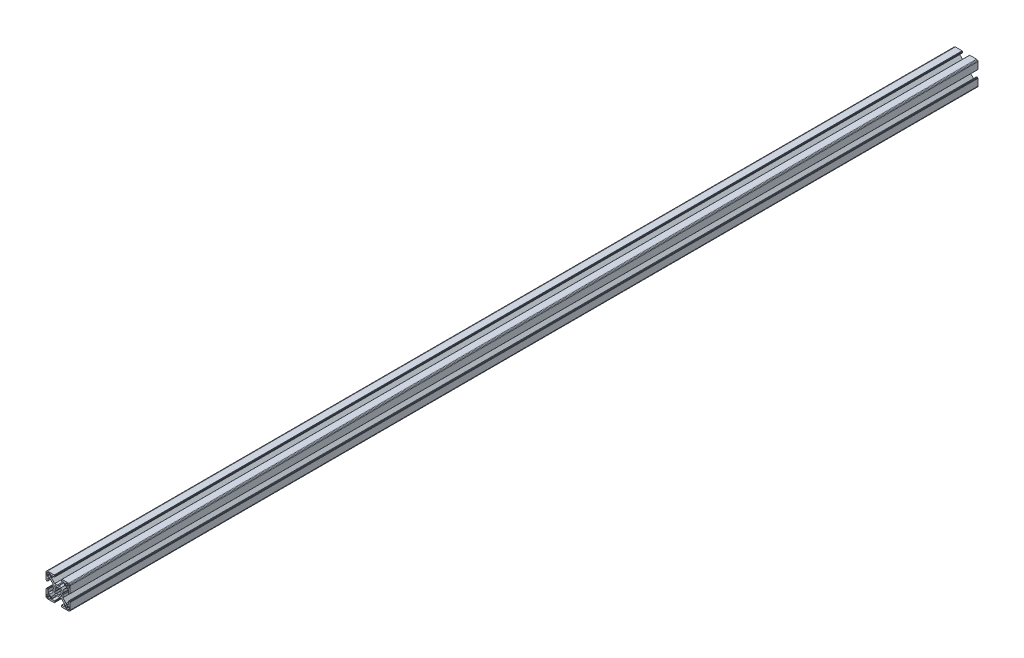
SolidWorks part; units mm, degrees
ref_plane "Front Plane" through (0, 0, 0) normal (0, 0, 1) x (1, 0, 0)
ref_plane "Top Plane" through (0, 0, 0) normal (0, 1, 0) x (1, 0, 0)
ref_plane "Right Plane" through (0, 0, 0) normal (1, 0, 0) x (0, 0, -1)
ref_plane "Plane1" through (0, 0, 0) normal (0, 0, 1) x (1, 0, 0)
sketch "Sketch1" plane through (0, 0, 0) normal (0, 0, 1) x (1, 0, 0)
  line L0 (28.3473, 29.9696) -> (28, 30)
  line L1 (28, 30) -> (19.75, 30)
  line L2 (19.75, 30) -> (19.7153, 29.997)
  line L3 (19.7153, 29.997) -> (19.6816, 29.9879)
  line L4 (19.6816, 29.9879) -> (19.65, 29.9732)
  line L5 (19.65, 29.9732) -> (19.6214, 29.9532)
  line L6 (19.6214, 29.9532) -> (19.5968, 29.9286)
  line L7 (19.5968, 29.9286) -> (19.5768, 29.9)
  line L8 (19.5768, 29.9) -> (19.5621, 29.8684)
  line L9 (19.5621, 29.8684) -> (19.553, 29.8347)
  line L10 (19.553, 29.8347) -> (19.55, 29.8)
  line L11 (19.55, 29.8) -> (19.55, 29.7)
  line L12 (19.55, 29.7) -> (19.547, 29.6653)
  line L13 (19.547, 29.6653) -> (19.5379, 29.6316)
  line L14 (19.5379, 29.6316) -> (19.5232, 29.6)
  line L15 (19.5232, 29.6) -> (19.5032, 29.5714)
  line L16 (19.5032, 29.5714) -> (19.4786, 29.5468)
  line L17 (19.4786, 29.5468) -> (19.45, 29.5268)
  line L18 (19.45, 29.5268) -> (19.4184, 29.5121)
  line L19 (19.4184, 29.5121) -> (19.3847, 29.503)
  line L20 (19.3847, 29.503) -> (19.35, 29.5)
  line L21 (19.35, 29.5) -> (19.25, 29.5)
  line L22 (19.25, 29.5) -> (19.2153, 29.497)
  line L23 (19.2153, 29.497) -> (19.1816, 29.4879)
  line L24 (19.1816, 29.4879) -> (19.15, 29.4732)
  line L25 (19.15, 29.4732) -> (19.1214, 29.4532)
  line L26 (19.1214, 29.4532) -> (19.0968, 29.4286)
  line L27 (19.0968, 29.4286) -> (19.0768, 29.4)
  line L28 (19.0768, 29.4) -> (19.0621, 29.3684)
  line L29 (19.0621, 29.3684) -> (19.053, 29.3347)
  line L30 (19.053, 29.3347) -> (19.05, 29.3)
  line L31 (19.05, 29.3) -> (19.05, 28.4)
  line L32 (19.05, 28.4) -> (19.0591, 28.2958)
  line L33 (19.0591, 28.2958) -> (19.0862, 28.1948)
  line L34 (19.0862, 28.1948) -> (19.1304, 28.1)
  line L35 (19.1304, 28.1) -> (19.1904, 28.0143)
  line L36 (19.1904, 28.0143) -> (19.2643, 27.9404)
  line L37 (19.2643, 27.9404) -> (19.35, 27.8804)
  line L38 (19.35, 27.8804) -> (19.4448, 27.8362)
  line L39 (19.4448, 27.8362) -> (19.5458, 27.8091)
  line L40 (19.5458, 27.8091) -> (19.65, 27.8)
  line L41 (19.65, 27.8) -> (23.05, 27.8)
  line L42 (23.05, 27.8) -> (23.0847, 27.7969)
  line L43 (23.0847, 27.7969) -> (23.1184, 27.7879)
  line L44 (23.1184, 27.7879) -> (23.15, 27.7732)
  line L45 (23.15, 27.7732) -> (23.1786, 27.7532)
  line L46 (23.1786, 27.7532) -> (23.2032, 27.7285)
  line L47 (23.2032, 27.7285) -> (23.2232, 27.7)
  line L48 (23.2232, 27.7) -> (23.2379, 27.6684)
  line L49 (23.2379, 27.6684) -> (23.247, 27.6347)
  line L50 (23.247, 27.6347) -> (23.25, 27.6)
  line L51 (23.25, 27.6) -> (23.25, 25.05)
  line L52 (23.25, 25.05) -> (19.2045, 21)
  line L53 (19.2045, 21) -> (15.9, 21)
  line L54 (15.9, 21) -> (15, 20.4848)
  line L55 (15, 20.4848) -> (14.1, 21)
  line L56 (14.1, 21) -> (10.7955, 21)
  line L57 (10.7955, 21) -> (7.9973, 23.8013)
  line L58 (7.9973, 23.8013) -> (6.75, 25.05)
  line L59 (6.75, 25.05) -> (6.75, 27.6)
  line L60 (6.75, 27.6) -> (6.753, 27.6347)
  line L61 (6.753, 27.6347) -> (6.7621, 27.6684)
  line L62 (6.7621, 27.6684) -> (6.7768, 27.7)
  line L63 (6.7768, 27.7) -> (6.7968, 27.7285)
  line L64 (6.7968, 27.7285) -> (6.8215, 27.7532)
  line L65 (6.8215, 27.7532) -> (6.85, 27.7732)
  line L66 (6.85, 27.7732) -> (6.8816, 27.7879)
  line L67 (6.8816, 27.7879) -> (6.9153, 27.7969)
  line L68 (6.9153, 27.7969) -> (6.95, 27.8)
  line L69 (6.95, 27.8) -> (10.35, 27.8)
  line L70 (10.35, 27.8) -> (10.4542, 27.8091)
  line L71 (10.4542, 27.8091) -> (10.5552, 27.8362)
  line L72 (10.5552, 27.8362) -> (10.65, 27.8804)
  line L73 (10.65, 27.8804) -> (10.7357, 27.9404)
  line L74 (10.7357, 27.9404) -> (10.8096, 28.0143)
  line L75 (10.8096, 28.0143) -> (10.8696, 28.1)
  line L76 (10.8696, 28.1) -> (10.9138, 28.1948)
  line L77 (10.9138, 28.1948) -> (10.9409, 28.2958)
  line L78 (10.9409, 28.2958) -> (10.95, 28.4)
  line L79 (10.95, 28.4) -> (10.95, 29.3)
  line L80 (10.95, 29.3) -> (10.947, 29.3347)
  line L81 (10.947, 29.3347) -> (10.938, 29.3684)
  line L82 (10.938, 29.3684) -> (10.9232, 29.4)
  line L83 (10.9232, 29.4) -> (10.9032, 29.4286)
  line L84 (10.9032, 29.4286) -> (10.8786, 29.4532)
  line L85 (10.8786, 29.4532) -> (10.85, 29.4732)
  line L86 (10.85, 29.4732) -> (10.8184, 29.4879)
  line L87 (10.8184, 29.4879) -> (10.7847, 29.497)
  line L88 (10.7847, 29.497) -> (10.75, 29.5)
  line L89 (10.75, 29.5) -> (10.65, 29.5)
  line L90 (10.65, 29.5) -> (10.6153, 29.503)
  line L91 (10.6153, 29.503) -> (10.5816, 29.5121)
  line L92 (10.5816, 29.5121) -> (10.55, 29.5268)
  line L93 (10.55, 29.5268) -> (10.5214, 29.5468)
  line L94 (10.5214, 29.5468) -> (10.4968, 29.5714)
  line L95 (10.4968, 29.5714) -> (10.4768, 29.6)
  line L96 (10.4768, 29.6) -> (10.4621, 29.6316)
  line L97 (10.4621, 29.6316) -> (10.453, 29.6653)
  line L98 (10.453, 29.6653) -> (10.45, 29.7)
  line L99 (10.45, 29.7) -> (10.45, 29.8)
  line L100 (10.45, 29.8) -> (10.447, 29.8347)
  line L101 (10.447, 29.8347) -> (10.4379, 29.8684)
  line L102 (10.4379, 29.8684) -> (10.4232, 29.9)
  line L103 (10.4232, 29.9) -> (10.4032, 29.9286)
  line L104 (10.4032, 29.9286) -> (10.3786, 29.9532)
  line L105 (10.3786, 29.9532) -> (10.35, 29.9732)
  line L106 (10.35, 29.9732) -> (10.3184, 29.9879)
  line L107 (10.3184, 29.9879) -> (10.2847, 29.997)
  line L108 (10.2847, 29.997) -> (10.25, 30)
  line L109 (10.25, 30) -> (2, 30)
  line L110 (2, 30) -> (1.6527, 29.9696)
  line L111 (1.6527, 29.9696) -> (1.316, 29.8794)
  line L112 (1.316, 29.8794) -> (1, 29.7321)
  line L113 (1, 29.7321) -> (0.7144, 29.5321)
  line L114 (0.7144, 29.5321) -> (0.4679, 29.2856)
  line L115 (0.4679, 29.2856) -> (0.2679, 29)
  line L116 (0.2679, 29) -> (0.1206, 28.684)
  line L117 (0.1206, 28.684) -> (0.0304, 28.3473)
  line L118 (0.0304, 28.3473) -> (0, 28)
  line L119 (0, 28) -> (0, 19.75)
  line L120 (0, 19.75) -> (0.003, 19.7153)
  line L121 (0.003, 19.7153) -> (0.0121, 19.6816)
  line L122 (0.0121, 19.6816) -> (0.0268, 19.65)
  line L123 (0.0268, 19.65) -> (0.0468, 19.6214)
  line L124 (0.0468, 19.6214) -> (0.0714, 19.5968)
  line L125 (0.0714, 19.5968) -> (0.1, 19.5768)
  line L126 (0.1, 19.5768) -> (0.1316, 19.5621)
  line L127 (0.1316, 19.5621) -> (0.1653, 19.553)
  line L128 (0.1653, 19.553) -> (0.2, 19.55)
  line L129 (0.2, 19.55) -> (0.3, 19.55)
  line L130 (0.3, 19.55) -> (0.3347, 19.547)
  line L131 (0.3347, 19.547) -> (0.3684, 19.5379)
  line L132 (0.3684, 19.5379) -> (0.4, 19.5232)
  line L133 (0.4, 19.5232) -> (0.4286, 19.5032)
  line L134 (0.4286, 19.5032) -> (0.4532, 19.4786)
  line L135 (0.4532, 19.4786) -> (0.4732, 19.45)
  line L136 (0.4732, 19.45) -> (0.4879, 19.4184)
  line L137 (0.4879, 19.4184) -> (0.497, 19.3847)
  line L138 (0.497, 19.3847) -> (0.5, 19.35)
  line L139 (0.5, 19.35) -> (0.5, 19.25)
  line L140 (0.5, 19.25) -> (0.503, 19.2153)
  line L141 (0.503, 19.2153) -> (0.5121, 19.1816)
  line L142 (0.5121, 19.1816) -> (0.5268, 19.15)
  line L143 (0.5268, 19.15) -> (0.5468, 19.1214)
  line L144 (0.5468, 19.1214) -> (0.5714, 19.0968)
  line L145 (0.5714, 19.0968) -> (0.6, 19.0768)
  line L146 (0.6, 19.0768) -> (0.6316, 19.0621)
  line L147 (0.6316, 19.0621) -> (0.6653, 19.053)
  line L148 (0.6653, 19.053) -> (0.7, 19.05)
  line L149 (0.7, 19.05) -> (1.6, 19.05)
  line L150 (1.6, 19.05) -> (1.7042, 19.0591)
  line L151 (1.7042, 19.0591) -> (1.8052, 19.0862)
  line L152 (1.8052, 19.0862) -> (1.9, 19.1304)
  line L153 (1.9, 19.1304) -> (1.9857, 19.1904)
  line L154 (1.9857, 19.1904) -> (2.0596, 19.2643)
  line L155 (2.0596, 19.2643) -> (2.1196, 19.35)
  line L156 (2.1196, 19.35) -> (2.1638, 19.4448)
  line L157 (2.1638, 19.4448) -> (2.1909, 19.5458)
  line L158 (2.1909, 19.5458) -> (2.2, 19.65)
  line L159 (2.2, 19.65) -> (2.2, 23.05)
  line L160 (2.2, 23.05) -> (2.203, 23.0847)
  line L161 (2.203, 23.0847) -> (2.2121, 23.1184)
  line L162 (2.2121, 23.1184) -> (2.2268, 23.15)
  line L163 (2.2268, 23.15) -> (2.2468, 23.1786)
  line L164 (2.2468, 23.1786) -> (2.2714, 23.2032)
  line L165 (2.2714, 23.2032) -> (2.3, 23.2232)
  line L166 (2.3, 23.2232) -> (2.3316, 23.2379)
  line L167 (2.3316, 23.2379) -> (2.3653, 23.247)
  line L168 (2.3653, 23.247) -> (2.4, 23.25)
  line L169 (2.4, 23.25) -> (4.95, 23.25)
  line L170 (4.95, 23.25) -> (7.9973, 20.2027)
  line L171 (7.9973, 20.2027) -> (8.9955, 19.2045)
  line L172 (8.9955, 19.2045) -> (8.9955, 15.9)
  line L173 (8.9955, 15.9) -> (9.5151, 15)
  line L174 (9.5151, 15) -> (8.9955, 14.1)
  line L175 (8.9955, 14.1) -> (8.9955, 10.7955)
  line L176 (8.9955, 10.7955) -> (4.95, 6.75)
  line L177 (4.95, 6.75) -> (2.4, 6.75)
  line L178 (2.4, 6.75) -> (2.3653, 6.753)
  line L179 (2.3653, 6.753) -> (2.3316, 6.7621)
  line L180 (2.3316, 6.7621) -> (2.3, 6.7768)
  line L181 (2.3, 6.7768) -> (2.2714, 6.7968)
  line L182 (2.2714, 6.7968) -> (2.2468, 6.8214)
  line L183 (2.2468, 6.8214) -> (2.2268, 6.85)
  line L184 (2.2268, 6.85) -> (2.2121, 6.8816)
  line L185 (2.2121, 6.8816) -> (2.203, 6.9153)
  line L186 (2.203, 6.9153) -> (2.2, 6.95)
  line L187 (2.2, 6.95) -> (2.2, 10.35)
  line L188 (2.2, 10.35) -> (2.1909, 10.4542)
  line L189 (2.1909, 10.4542) -> (2.1638, 10.5552)
  line L190 (2.1638, 10.5552) -> (2.1196, 10.65)
  line L191 (2.1196, 10.65) -> (2.0596, 10.7357)
  line L192 (2.0596, 10.7357) -> (1.9857, 10.8096)
  line L193 (1.9857, 10.8096) -> (1.9, 10.8696)
  line L194 (1.9, 10.8696) -> (1.8052, 10.9138)
  line L195 (1.8052, 10.9138) -> (1.7042, 10.9409)
  line L196 (1.7042, 10.9409) -> (1.6, 10.95)
  line L197 (1.6, 10.95) -> (0.7, 10.95)
  line L198 (0.7, 10.95) -> (0.6653, 10.9469)
  line L199 (0.6653, 10.9469) -> (0.6316, 10.9379)
  line L200 (0.6316, 10.9379) -> (0.6, 10.9232)
  line L201 (0.6, 10.9232) -> (0.5715, 10.9032)
  line L202 (0.5715, 10.9032) -> (0.5468, 10.8785)
  line L203 (0.5468, 10.8785) -> (0.5268, 10.85)
  line L204 (0.5268, 10.85) -> (0.5121, 10.8184)
  line L205 (0.5121, 10.8184) -> (0.503, 10.7847)
  line L206 (0.503, 10.7847) -> (0.5, 10.75)
  line L207 (0.5, 10.75) -> (0.5, 10.65)
  line L208 (0.5, 10.65) -> (0.497, 10.6153)
  line L209 (0.497, 10.6153) -> (0.4879, 10.5816)
  line L210 (0.4879, 10.5816) -> (0.4732, 10.55)
  line L211 (0.4732, 10.55) -> (0.4532, 10.5214)
  line L212 (0.4532, 10.5214) -> (0.4286, 10.4968)
  line L213 (0.4286, 10.4968) -> (0.4, 10.4768)
  line L214 (0.4, 10.4768) -> (0.3684, 10.4621)
  line L215 (0.3684, 10.4621) -> (0.3347, 10.453)
  line L216 (0.3347, 10.453) -> (0.3, 10.45)
  line L217 (0.3, 10.45) -> (0.2, 10.45)
  line L218 (0.2, 10.45) -> (0.1653, 10.447)
  line L219 (0.1653, 10.447) -> (0.1316, 10.4379)
  line L220 (0.1316, 10.4379) -> (0.1, 10.4232)
  line L221 (0.1, 10.4232) -> (0.0714, 10.4032)
  line L222 (0.0714, 10.4032) -> (0.0468, 10.3786)
  line L223 (0.0468, 10.3786) -> (0.0268, 10.35)
  line L224 (0.0268, 10.35) -> (0.0121, 10.3184)
  line L225 (0.0121, 10.3184) -> (0.003, 10.2847)
  line L226 (0.003, 10.2847) -> (0, 10.25)
  line L227 (0, 10.25) -> (0, 2)
  line L228 (0, 2) -> (0.0304, 1.6527)
  line L229 (0.0304, 1.6527) -> (0.1206, 1.316)
  line L230 (0.1206, 1.316) -> (0.2679, 1)
  line L231 (0.2679, 1) -> (0.4679, 0.7144)
  line L232 (0.4679, 0.7144) -> (0.7144, 0.4679)
  line L233 (0.7144, 0.4679) -> (1, 0.2679)
  line L234 (1, 0.2679) -> (1.316, 0.1206)
  line L235 (1.316, 0.1206) -> (1.6527, 0.0304)
  line L236 (1.6527, 0.0304) -> (2, 0)
  line L237 (2, 0) -> (10.25, 0)
  line L238 (10.25, 0) -> (10.2847, 0.003)
  line L239 (10.2847, 0.003) -> (10.3184, 0.0121)
  line L240 (10.3184, 0.0121) -> (10.35, 0.0268)
  line L241 (10.35, 0.0268) -> (10.3786, 0.0468)
  line L242 (10.3786, 0.0468) -> (10.4032, 0.0714)
  line L243 (10.4032, 0.0714) -> (10.4232, 0.1)
  line L244 (10.4232, 0.1) -> (10.4379, 0.1316)
  line L245 (10.4379, 0.1316) -> (10.447, 0.1653)
  line L246 (10.447, 0.1653) -> (10.45, 0.2)
  line L247 (10.45, 0.2) -> (10.45, 0.3)
  line L248 (10.45, 0.3) -> (10.453, 0.3347)
  line L249 (10.453, 0.3347) -> (10.4621, 0.3684)
  line L250 (10.4621, 0.3684) -> (10.4768, 0.4)
  line L251 (10.4768, 0.4) -> (10.4968, 0.4286)
  line L252 (10.4968, 0.4286) -> (10.5214, 0.4532)
  line L253 (10.5214, 0.4532) -> (10.55, 0.4732)
  line L254 (10.55, 0.4732) -> (10.5816, 0.4879)
  line L255 (10.5816, 0.4879) -> (10.6153, 0.497)
  line L256 (10.6153, 0.497) -> (10.65, 0.5)
  line L257 (10.65, 0.5) -> (10.75, 0.5)
  line L258 (10.75, 0.5) -> (10.7847, 0.503)
  line L259 (10.7847, 0.503) -> (10.8184, 0.5121)
  line L260 (10.8184, 0.5121) -> (10.85, 0.5268)
  line L261 (10.85, 0.5268) -> (10.8785, 0.5468)
  line L262 (10.8785, 0.5468) -> (10.9032, 0.5715)
  line L263 (10.9032, 0.5715) -> (10.9232, 0.6)
  line L264 (10.9232, 0.6) -> (10.9379, 0.6316)
  line L265 (10.9379, 0.6316) -> (10.9469, 0.6653)
  line L266 (10.9469, 0.6653) -> (10.95, 0.7)
  line L267 (10.95, 0.7) -> (10.95, 1.6)
  line L268 (10.95, 1.6) -> (10.9409, 1.7042)
  line L269 (10.9409, 1.7042) -> (10.9138, 1.8052)
  line L270 (10.9138, 1.8052) -> (10.8696, 1.9)
  line L271 (10.8696, 1.9) -> (10.8096, 1.9857)
  line L272 (10.8096, 1.9857) -> (10.7357, 2.0596)
  line L273 (10.7357, 2.0596) -> (10.65, 2.1196)
  line L274 (10.65, 2.1196) -> (10.5552, 2.1638)
  line L275 (10.5552, 2.1638) -> (10.4542, 2.1909)
  line L276 (10.4542, 2.1909) -> (10.35, 2.2)
  line L277 (10.35, 2.2) -> (6.95, 2.2)
  line L278 (6.95, 2.2) -> (6.9153, 2.203)
  line L279 (6.9153, 2.203) -> (6.8816, 2.212)
  line L280 (6.8816, 2.212) -> (6.85, 2.2268)
  line L281 (6.85, 2.2268) -> (6.8215, 2.2468)
  line L282 (6.8215, 2.2468) -> (6.7968, 2.2714)
  line L283 (6.7968, 2.2714) -> (6.7768, 2.3)
  line L284 (6.7768, 2.3) -> (6.7621, 2.3316)
  line L285 (6.7621, 2.3316) -> (6.753, 2.3653)
  line L286 (6.753, 2.3653) -> (6.75, 2.4)
  line L287 (6.75, 2.4) -> (6.75, 4.95)
  line L288 (6.75, 4.95) -> (9.7875, 7.9908)
  line L289 (9.7875, 7.9908) -> (10.7955, 9)
  line L290 (10.7955, 9) -> (14.1, 9)
  line L291 (14.1, 9) -> (15, 9.5151)
  line L292 (15, 9.5151) -> (15.9, 9)
  line L293 (15.9, 9) -> (19.2045, 9)
  line L294 (19.2045, 9) -> (20.2126, 7.9908)
  line L295 (20.2126, 7.9908) -> (23.25, 4.95)
  line L296 (23.25, 4.95) -> (23.25, 2.4)
  line L297 (23.25, 2.4) -> (23.247, 2.3653)
  line L298 (23.247, 2.3653) -> (23.2379, 2.3316)
  line L299 (23.2379, 2.3316) -> (23.2232, 2.3)
  line L300 (23.2232, 2.3) -> (23.2032, 2.2714)
  line L301 (23.2032, 2.2714) -> (23.1786, 2.2468)
  line L302 (23.1786, 2.2468) -> (23.15, 2.2268)
  line L303 (23.15, 2.2268) -> (23.1184, 2.212)
  line L304 (23.1184, 2.212) -> (23.0847, 2.203)
  line L305 (23.0847, 2.203) -> (23.05, 2.2)
  line L306 (23.05, 2.2) -> (19.65, 2.2)
  line L307 (19.65, 2.2) -> (19.5458, 2.1909)
  line L308 (19.5458, 2.1909) -> (19.4448, 2.1638)
  line L309 (19.4448, 2.1638) -> (19.35, 2.1196)
  line L310 (19.35, 2.1196) -> (19.2643, 2.0596)
  line L311 (19.2643, 2.0596) -> (19.1904, 1.9857)
  line L312 (19.1904, 1.9857) -> (19.1304, 1.9)
  line L313 (19.1304, 1.9) -> (19.0862, 1.8052)
  line L314 (19.0862, 1.8052) -> (19.0591, 1.7042)
  line L315 (19.0591, 1.7042) -> (19.05, 1.6)
  line L316 (19.05, 1.6) -> (19.05, 0.7)
  line L317 (19.05, 0.7) -> (19.053, 0.6653)
  line L318 (19.053, 0.6653) -> (19.0621, 0.6316)
  line L319 (19.0621, 0.6316) -> (19.0768, 0.6)
  line L320 (19.0768, 0.6) -> (19.0968, 0.5714)
  line L321 (19.0968, 0.5714) -> (19.1214, 0.5468)
  line L322 (19.1214, 0.5468) -> (19.15, 0.5268)
  line L323 (19.15, 0.5268) -> (19.1816, 0.5121)
  line L324 (19.1816, 0.5121) -> (19.2153, 0.503)
  line L325 (19.2153, 0.503) -> (19.25, 0.5)
  line L326 (19.25, 0.5) -> (19.35, 0.5)
  line L327 (19.35, 0.5) -> (19.3847, 0.497)
  line L328 (19.3847, 0.497) -> (19.4184, 0.4879)
  line L329 (19.4184, 0.4879) -> (19.45, 0.4732)
  line L330 (19.45, 0.4732) -> (19.4786, 0.4532)
  line L331 (19.4786, 0.4532) -> (19.5032, 0.4286)
  line L332 (19.5032, 0.4286) -> (19.5232, 0.4)
  line L333 (19.5232, 0.4) -> (19.5379, 0.3684)
  line L334 (19.5379, 0.3684) -> (19.547, 0.3347)
  line L335 (19.547, 0.3347) -> (19.55, 0.3)
  line L336 (19.55, 0.3) -> (19.55, 0.2)
  line L337 (19.55, 0.2) -> (19.553, 0.1653)
  line L338 (19.553, 0.1653) -> (19.5621, 0.1316)
  line L339 (19.5621, 0.1316) -> (19.5768, 0.1)
  line L340 (19.5768, 0.1) -> (19.5968, 0.0714)
  line L341 (19.5968, 0.0714) -> (19.6214, 0.0468)
  line L342 (19.6214, 0.0468) -> (19.65, 0.0268)
  line L343 (19.65, 0.0268) -> (19.6816, 0.0121)
  line L344 (19.6816, 0.0121) -> (19.7153, 0.003)
  line L345 (19.7153, 0.003) -> (19.75, 0)
  line L346 (19.75, 0) -> (28, 0)
  line L347 (28, 0) -> (28.3473, 0.0304)
  line L348 (28.3473, 0.0304) -> (28.684, 0.1206)
  line L349 (28.684, 0.1206) -> (29, 0.2679)
  line L350 (29, 0.2679) -> (29.2856, 0.4679)
  line L351 (29.2856, 0.4679) -> (29.5321, 0.7144)
  line L352 (29.5321, 0.7144) -> (29.7321, 1)
  line L353 (29.7321, 1) -> (29.8794, 1.316)
  line L354 (29.8794, 1.316) -> (29.9696, 1.6527)
  line L355 (29.9696, 1.6527) -> (30, 2)
  line L356 (30, 2) -> (30, 10.25)
  line L357 (30, 10.25) -> (29.997, 10.2847)
  line L358 (29.997, 10.2847) -> (29.988, 10.3184)
  line L359 (29.988, 10.3184) -> (29.9732, 10.35)
  line L360 (29.9732, 10.35) -> (29.9532, 10.3785)
  line L361 (29.9532, 10.3785) -> (29.9286, 10.4032)
  line L362 (29.9286, 10.4032) -> (29.9, 10.4232)
  line L363 (29.9, 10.4232) -> (29.8684, 10.4379)
  line L364 (29.8684, 10.4379) -> (29.8347, 10.447)
  line L365 (29.8347, 10.447) -> (29.8, 10.45)
  line L366 (29.8, 10.45) -> (29.7, 10.45)
  line L367 (29.7, 10.45) -> (29.6649, 10.4534)
  line L368 (29.6649, 10.4534) -> (29.6312, 10.4624)
  line L369 (29.6312, 10.4624) -> (29.5996, 10.4772)
  line L370 (29.5996, 10.4772) -> (29.5711, 10.4972)
  line L371 (29.5711, 10.4972) -> (29.5464, 10.5218)
  line L372 (29.5464, 10.5218) -> (29.5264, 10.5504)
  line L373 (29.5264, 10.5504) -> (29.5117, 10.582)
  line L374 (29.5117, 10.582) -> (29.5027, 10.6156)
  line L375 (29.5027, 10.6156) -> (29.4996, 10.6504)
  line L376 (29.4996, 10.6504) -> (29.4996, 10.7504)
  line L377 (29.4996, 10.7504) -> (29.497, 10.7847)
  line L378 (29.497, 10.7847) -> (29.4879, 10.8184)
  line L379 (29.4879, 10.8184) -> (29.4732, 10.85)
  line L380 (29.4732, 10.85) -> (29.4532, 10.8785)
  line L381 (29.4532, 10.8785) -> (29.4286, 10.9032)
  line L382 (29.4286, 10.9032) -> (29.4, 10.9232)
  line L383 (29.4, 10.9232) -> (29.3684, 10.9379)
  line L384 (29.3684, 10.9379) -> (29.3347, 10.9469)
  line L385 (29.3347, 10.9469) -> (29.3, 10.95)
  line L386 (29.3, 10.95) -> (28.4, 10.95)
  line L387 (28.4, 10.95) -> (28.2958, 10.9409)
  line L388 (28.2958, 10.9409) -> (28.1948, 10.9138)
  line L389 (28.1948, 10.9138) -> (28.1, 10.8696)
  line L390 (28.1, 10.8696) -> (28.0143, 10.8096)
  line L391 (28.0143, 10.8096) -> (27.9404, 10.7357)
  line L392 (27.9404, 10.7357) -> (27.8804, 10.65)
  line L393 (27.8804, 10.65) -> (27.8362, 10.5552)
  line L394 (27.8362, 10.5552) -> (27.8091, 10.4542)
  line L395 (27.8091, 10.4542) -> (27.8, 10.35)
  line L396 (27.8, 10.35) -> (27.8, 6.95)
  line L397 (27.8, 6.95) -> (27.797, 6.9153)
  line L398 (27.797, 6.9153) -> (27.7879, 6.8816)
  line L399 (27.7879, 6.8816) -> (27.7732, 6.85)
  line L400 (27.7732, 6.85) -> (27.7532, 6.8214)
  line L401 (27.7532, 6.8214) -> (27.7286, 6.7968)
  line L402 (27.7286, 6.7968) -> (27.7, 6.7768)
  line L403 (27.7, 6.7768) -> (27.6684, 6.7621)
  line L404 (27.6684, 6.7621) -> (27.6347, 6.753)
  line L405 (27.6347, 6.753) -> (27.6, 6.75)
  line L406 (27.6, 6.75) -> (25.05, 6.75)
  line L407 (25.05, 6.75) -> (23.8092, 7.9908)
  line L408 (23.8092, 7.9908) -> (21.0045, 10.7955)
  line L409 (21.0045, 10.7955) -> (21.0045, 14.1)
  line L410 (21.0045, 14.1) -> (20.4849, 15)
  line L411 (20.4849, 15) -> (21.0045, 15.9)
  line L412 (21.0045, 15.9) -> (21.0045, 19.2045)
  line L413 (21.0045, 19.2045) -> (25.05, 23.25)
  line L414 (25.05, 23.25) -> (27.6, 23.25)
  line L415 (27.6, 23.25) -> (27.6347, 23.247)
  line L416 (27.6347, 23.247) -> (27.6684, 23.2379)
  line L417 (27.6684, 23.2379) -> (27.7, 23.2232)
  line L418 (27.7, 23.2232) -> (27.7286, 23.2032)
  line L419 (27.7286, 23.2032) -> (27.7532, 23.1786)
  line L420 (27.7532, 23.1786) -> (27.7732, 23.15)
  line L421 (27.7732, 23.15) -> (27.7879, 23.1184)
  line L422 (27.7879, 23.1184) -> (27.797, 23.0847)
  line L423 (27.797, 23.0847) -> (27.8, 23.05)
  line L424 (27.8, 23.05) -> (27.8, 19.65)
  line L425 (27.8, 19.65) -> (27.8091, 19.5458)
  line L426 (27.8091, 19.5458) -> (27.8362, 19.4448)
  line L427 (27.8362, 19.4448) -> (27.8804, 19.35)
  line L428 (27.8804, 19.35) -> (27.9404, 19.2643)
  line L429 (27.9404, 19.2643) -> (28.0143, 19.1904)
  line L430 (28.0143, 19.1904) -> (28.1, 19.1304)
  line L431 (28.1, 19.1304) -> (28.1948, 19.0862)
  line L432 (28.1948, 19.0862) -> (28.2958, 19.0591)
  line L433 (28.2958, 19.0591) -> (28.4, 19.05)
  line L434 (28.4, 19.05) -> (29.3, 19.05)
  line L435 (29.3, 19.05) -> (29.3347, 19.053)
  line L436 (29.3347, 19.053) -> (29.3684, 19.0621)
  line L437 (29.3684, 19.0621) -> (29.4, 19.0768)
  line L438 (29.4, 19.0768) -> (29.4282, 19.0971)
  line L439 (29.4282, 19.0971) -> (29.4528, 19.1218)
  line L440 (29.4528, 19.1218) -> (29.4728, 19.1504)
  line L441 (29.4728, 19.1504) -> (29.4876, 19.182)
  line L442 (29.4876, 19.182) -> (29.4966, 19.2156)
  line L443 (29.4966, 19.2156) -> (29.4996, 19.2504)
  line L444 (29.4996, 19.2504) -> (29.4996, 19.3504)
  line L445 (29.4996, 19.3504) -> (29.5027, 19.3851)
  line L446 (29.5027, 19.3851) -> (29.5117, 19.4188)
  line L447 (29.5117, 19.4188) -> (29.5264, 19.4504)
  line L448 (29.5264, 19.4504) -> (29.5464, 19.4789)
  line L449 (29.5464, 19.4789) -> (29.5711, 19.5036)
  line L450 (29.5711, 19.5036) -> (29.5996, 19.5236)
  line L451 (29.5996, 19.5236) -> (29.6312, 19.5383)
  line L452 (29.6312, 19.5383) -> (29.6649, 19.5473)
  line L453 (29.6649, 19.5473) -> (29.7, 19.55)
  line L454 (29.7, 19.55) -> (29.8, 19.55)
  line L455 (29.8, 19.55) -> (29.8347, 19.553)
  line L456 (29.8347, 19.553) -> (29.8684, 19.5621)
  line L457 (29.8684, 19.5621) -> (29.9, 19.5768)
  line L458 (29.9, 19.5768) -> (29.9286, 19.5968)
  line L459 (29.9286, 19.5968) -> (29.9532, 19.6214)
  line L460 (29.9532, 19.6214) -> (29.9732, 19.65)
  line L461 (29.9732, 19.65) -> (29.9879, 19.6816)
  line L462 (29.9879, 19.6816) -> (29.997, 19.7153)
  line L463 (29.997, 19.7153) -> (30, 19.75)
  line L464 (30, 19.75) -> (30, 28)
  line L465 (30, 28) -> (29.9696, 28.3473)
  line L466 (29.9696, 28.3473) -> (29.8794, 28.684)
  line L467 (29.8794, 28.684) -> (29.7321, 29)
  line L468 (29.7321, 29) -> (29.5321, 29.2856)
  line L469 (29.5321, 29.2856) -> (29.2856, 29.5321)
  line L470 (29.2856, 29.5321) -> (29, 29.7321)
  line L471 (29, 29.7321) -> (28.684, 29.8794)
  line L472 (28.684, 29.8794) -> (28.3473, 29.9696)
  line L473 (1.3, 25.5) -> (1.3, 27.7)
  line L474 (1.3, 27.7) -> (1.3123, 27.8564)
  line L475 (1.3123, 27.8564) -> (1.3489, 28.009)
  line L476 (1.3489, 28.009) -> (1.409, 28.154)
  line L477 (1.409, 28.154) -> (1.491, 28.2878)
  line L478 (1.491, 28.2878) -> (1.5929, 28.4071)
  line L479 (1.5929, 28.4071) -> (1.7122, 28.509)
  line L480 (1.7122, 28.509) -> (1.846, 28.591)
  line L481 (1.846, 28.591) -> (1.991, 28.6511)
  line L482 (1.991, 28.6511) -> (2.1436, 28.6877)
  line L483 (2.1436, 28.6877) -> (2.3, 28.7)
  line L484 (2.3, 28.7) -> (4.5, 28.7)
  line L485 (4.5, 28.7) -> (4.6564, 28.6877)
  line L486 (4.6564, 28.6877) -> (4.809, 28.6511)
  line L487 (4.809, 28.6511) -> (4.954, 28.591)
  line L488 (4.954, 28.591) -> (5.0878, 28.509)
  line L489 (5.0878, 28.509) -> (5.2071, 28.4071)
  line L490 (5.2071, 28.4071) -> (5.309, 28.2878)
  line L491 (5.309, 28.2878) -> (5.391, 28.154)
  line L492 (5.391, 28.154) -> (5.4511, 28.009)
  line L493 (5.4511, 28.009) -> (5.4877, 27.8564)
  line L494 (5.4877, 27.8564) -> (5.5, 27.7)
  line L495 (5.5, 27.7) -> (5.5, 25.5)
  line L496 (5.5, 25.5) -> (5.4877, 25.3436)
  line L497 (5.4877, 25.3436) -> (5.4511, 25.191)
  line L498 (5.4511, 25.191) -> (5.391, 25.046)
  line L499 (5.391, 25.046) -> (5.309, 24.9122)
  line L500 (5.309, 24.9122) -> (5.2071, 24.7929)
  line L501 (5.2071, 24.7929) -> (5.0878, 24.691)
  line L502 (5.0878, 24.691) -> (4.954, 24.609)
  line L503 (4.954, 24.609) -> (4.809, 24.5489)
  line L504 (4.809, 24.5489) -> (4.6564, 24.5123)
  line L505 (4.6564, 24.5123) -> (4.5, 24.5)
  line L506 (4.5, 24.5) -> (2.3, 24.5)
  line L507 (2.3, 24.5) -> (2.1436, 24.5123)
  line L508 (2.1436, 24.5123) -> (1.991, 24.5489)
  line L509 (1.991, 24.5489) -> (1.846, 24.609)
  line L510 (1.846, 24.609) -> (1.7122, 24.691)
  line L511 (1.7122, 24.691) -> (1.5929, 24.7929)
  line L512 (1.5929, 24.7929) -> (1.491, 24.9122)
  line L513 (1.491, 24.9122) -> (1.409, 25.046)
  line L514 (1.409, 25.046) -> (1.3489, 25.191)
  line L515 (1.3489, 25.191) -> (1.3123, 25.3436)
  line L516 (1.3123, 25.3436) -> (1.3, 25.5)
  line L517 (25.3436, 28.6877) -> (25.5, 28.7)
  line L518 (25.5, 28.7) -> (27.7, 28.7)
  line L519 (27.7, 28.7) -> (27.8564, 28.6877)
  line L520 (27.8564, 28.6877) -> (28.009, 28.6511)
  line L521 (28.009, 28.6511) -> (28.154, 28.591)
  line L522 (28.154, 28.591) -> (28.2878, 28.509)
  line L523 (28.2878, 28.509) -> (28.4071, 28.4071)
  line L524 (28.4071, 28.4071) -> (28.509, 28.2878)
  line L525 (28.509, 28.2878) -> (28.591, 28.154)
  line L526 (28.591, 28.154) -> (28.6511, 28.009)
  line L527 (28.6511, 28.009) -> (28.6877, 27.8564)
  line L528 (28.6877, 27.8564) -> (28.7, 27.7)
  line L529 (28.7, 27.7) -> (28.7, 25.5)
  line L530 (28.7, 25.5) -> (28.6877, 25.3436)
  line L531 (28.6877, 25.3436) -> (28.6511, 25.191)
  line L532 (28.6511, 25.191) -> (28.591, 25.046)
  line L533 (28.591, 25.046) -> (28.509, 24.9122)
  line L534 (28.509, 24.9122) -> (28.4071, 24.7929)
  line L535 (28.4071, 24.7929) -> (28.2878, 24.691)
  line L536 (28.2878, 24.691) -> (28.154, 24.609)
  line L537 (28.154, 24.609) -> (28.009, 24.5489)
  line L538 (28.009, 24.5489) -> (27.8564, 24.5123)
  line L539 (27.8564, 24.5123) -> (27.7, 24.5)
  line L540 (27.7, 24.5) -> (25.5, 24.5)
  line L541 (25.5, 24.5) -> (25.3436, 24.5123)
  line L542 (25.3436, 24.5123) -> (25.191, 24.5489)
  line L543 (25.191, 24.5489) -> (25.046, 24.609)
  line L544 (25.046, 24.609) -> (24.9122, 24.691)
  line L545 (24.9122, 24.691) -> (24.7929, 24.7929)
  line L546 (24.7929, 24.7929) -> (24.691, 24.9122)
  line L547 (24.691, 24.9122) -> (24.609, 25.046)
  line L548 (24.609, 25.046) -> (24.5489, 25.191)
  line L549 (24.5489, 25.191) -> (24.5123, 25.3436)
  line L550 (24.5123, 25.3436) -> (24.5, 25.5)
  line L551 (24.5, 25.5) -> (24.5, 27.7)
  line L552 (24.5, 27.7) -> (24.5123, 27.8564)
  line L553 (24.5123, 27.8564) -> (24.5489, 28.009)
  line L554 (24.5489, 28.009) -> (24.609, 28.154)
  line L555 (24.609, 28.154) -> (24.691, 28.2878)
  line L556 (24.691, 28.2878) -> (24.7929, 28.4071)
  line L557 (24.7929, 28.4071) -> (24.9122, 28.509)
  line L558 (24.9122, 28.509) -> (25.046, 28.591)
  line L559 (25.046, 28.591) -> (25.191, 28.6511)
  line L560 (25.191, 28.6511) -> (25.3436, 28.6877)
  line L561 (15, 18.65) -> (15.55, 18.6083)
  line L562 (15.55, 18.6083) -> (16.0875, 18.4842)
  line L563 (16.0875, 18.4842) -> (16.6001, 18.2806)
  line L564 (16.6001, 18.2806) -> (18.1359, 19.5184)
  line L565 (18.1359, 19.5184) -> (18.645, 19.1187)
  line L566 (18.645, 19.1187) -> (19.1036, 18.6621)
  line L567 (19.1036, 18.6621) -> (19.5053, 18.1547)
  line L568 (19.5053, 18.1547) -> (18.2806, 16.6001)
  line L569 (18.2806, 16.6001) -> (18.4842, 16.0875)
  line L570 (18.4842, 16.0875) -> (18.6083, 15.55)
  line L571 (18.6083, 15.55) -> (18.65, 15)
  line L572 (18.65, 15) -> (18.6083, 14.45)
  line L573 (18.6083, 14.45) -> (18.4842, 13.9125)
  line L574 (18.4842, 13.9125) -> (18.2806, 13.3999)
  line L575 (18.2806, 13.3999) -> (19.5053, 11.8453)
  line L576 (19.5053, 11.8453) -> (19.1036, 11.3379)
  line L577 (19.1036, 11.3379) -> (18.645, 10.8813)
  line L578 (18.645, 10.8813) -> (18.1359, 10.4816)
  line L579 (18.1359, 10.4816) -> (16.6001, 11.7194)
  line L580 (16.6001, 11.7194) -> (16.0875, 11.5158)
  line L581 (16.0875, 11.5158) -> (15.55, 11.3917)
  line L582 (15.55, 11.3917) -> (15, 11.35)
  line L583 (15, 11.35) -> (14.45, 11.3917)
  line L584 (14.45, 11.3917) -> (13.9125, 11.5158)
  line L585 (13.9125, 11.5158) -> (13.3999, 11.7194)
  line L586 (13.3999, 11.7194) -> (11.8641, 10.4816)
  line L587 (11.8641, 10.4816) -> (11.355, 10.8813)
  line L588 (11.355, 10.8813) -> (10.8964, 11.3379)
  line L589 (10.8964, 11.3379) -> (10.4947, 11.8453)
  line L590 (10.4947, 11.8453) -> (11.7194, 13.3999)
  line L591 (11.7194, 13.3999) -> (11.5158, 13.9125)
  line L592 (11.5158, 13.9125) -> (11.3917, 14.45)
  line L593 (11.3917, 14.45) -> (11.35, 15)
  line L594 (11.35, 15) -> (11.3917, 15.55)
  line L595 (11.3917, 15.55) -> (11.5158, 16.0875)
  line L596 (11.5158, 16.0875) -> (11.7194, 16.6001)
  line L597 (11.7194, 16.6001) -> (10.4947, 18.1547)
  line L598 (10.4947, 18.1547) -> (10.8964, 18.6621)
  line L599 (10.8964, 18.6621) -> (11.355, 19.1187)
  line L600 (11.355, 19.1187) -> (11.8641, 19.5184)
  line L601 (11.8641, 19.5184) -> (13.3999, 18.2806)
  line L602 (13.3999, 18.2806) -> (13.9125, 18.4842)
  line L603 (13.9125, 18.4842) -> (14.45, 18.6083)
  line L604 (14.45, 18.6083) -> (15, 18.65)
  line L605 (4.5, 1.3) -> (2.3, 1.3)
  line L606 (2.3, 1.3) -> (2.1436, 1.3123)
  line L607 (2.1436, 1.3123) -> (1.991, 1.3489)
  line L608 (1.991, 1.3489) -> (1.846, 1.409)
  line L609 (1.846, 1.409) -> (1.7122, 1.491)
  line L610 (1.7122, 1.491) -> (1.5929, 1.5929)
  line L611 (1.5929, 1.5929) -> (1.491, 1.7122)
  line L612 (1.491, 1.7122) -> (1.409, 1.846)
  line L613 (1.409, 1.846) -> (1.3489, 1.991)
  line L614 (1.3489, 1.991) -> (1.3123, 2.1436)
  line L615 (1.3123, 2.1436) -> (1.3, 2.3)
  line L616 (1.3, 2.3) -> (1.3, 4.5)
  line L617 (1.3, 4.5) -> (1.3123, 4.6564)
  line L618 (1.3123, 4.6564) -> (1.3489, 4.809)
  line L619 (1.3489, 4.809) -> (1.409, 4.954)
  line L620 (1.409, 4.954) -> (1.491, 5.0878)
  line L621 (1.491, 5.0878) -> (1.5929, 5.2071)
  line L622 (1.5929, 5.2071) -> (1.7122, 5.309)
  line L623 (1.7122, 5.309) -> (1.846, 5.391)
  line L624 (1.846, 5.391) -> (1.991, 5.4511)
  line L625 (1.991, 5.4511) -> (2.1436, 5.4877)
  line L626 (2.1436, 5.4877) -> (2.3, 5.5)
  line L627 (2.3, 5.5) -> (4.5, 5.5)
  line L628 (4.5, 5.5) -> (4.6564, 5.4877)
  line L629 (4.6564, 5.4877) -> (4.809, 5.4511)
  line L630 (4.809, 5.4511) -> (4.954, 5.391)
  line L631 (4.954, 5.391) -> (5.0878, 5.309)
  line L632 (5.0878, 5.309) -> (5.2071, 5.2071)
  line L633 (5.2071, 5.2071) -> (5.309, 5.0878)
  line L634 (5.309, 5.0878) -> (5.391, 4.954)
  line L635 (5.391, 4.954) -> (5.4511, 4.809)
  line L636 (5.4511, 4.809) -> (5.4877, 4.6564)
  line L637 (5.4877, 4.6564) -> (5.5, 4.5)
  line L638 (5.5, 4.5) -> (5.5, 2.3)
  line L639 (5.5, 2.3) -> (5.4877, 2.1436)
  line L640 (5.4877, 2.1436) -> (5.4511, 1.991)
  line L641 (5.4511, 1.991) -> (5.391, 1.846)
  line L642 (5.391, 1.846) -> (5.309, 1.7122)
  line L643 (5.309, 1.7122) -> (5.2071, 1.5929)
  line L644 (5.2071, 1.5929) -> (5.0878, 1.491)
  line L645 (5.0878, 1.491) -> (4.954, 1.409)
  line L646 (4.954, 1.409) -> (4.809, 1.3489)
  line L647 (4.809, 1.3489) -> (4.6564, 1.3123)
  line L648 (4.6564, 1.3123) -> (4.5, 1.3)
  line L649 (27.7, 1.3) -> (25.5, 1.3)
  line L650 (25.5, 1.3) -> (25.3436, 1.3123)
  line L651 (25.3436, 1.3123) -> (25.191, 1.3489)
  line L652 (25.191, 1.3489) -> (25.046, 1.409)
  line L653 (25.046, 1.409) -> (24.9122, 1.491)
  line L654 (24.9122, 1.491) -> (24.7929, 1.5929)
  line L655 (24.7929, 1.5929) -> (24.691, 1.7122)
  line L656 (24.691, 1.7122) -> (24.609, 1.846)
  line L657 (24.609, 1.846) -> (24.5489, 1.991)
  line L658 (24.5489, 1.991) -> (24.5123, 2.1436)
  line L659 (24.5123, 2.1436) -> (24.5, 2.3)
  line L660 (24.5, 2.3) -> (24.5, 4.5)
  line L661 (24.5, 4.5) -> (24.5123, 4.6564)
  line L662 (24.5123, 4.6564) -> (24.5489, 4.809)
  line L663 (24.5489, 4.809) -> (24.609, 4.954)
  line L664 (24.609, 4.954) -> (24.691, 5.0878)
  line L665 (24.691, 5.0878) -> (24.7929, 5.2071)
  line L666 (24.7929, 5.2071) -> (24.9122, 5.309)
  line L667 (24.9122, 5.309) -> (25.046, 5.391)
  line L668 (25.046, 5.391) -> (25.191, 5.4511)
  line L669 (25.191, 5.4511) -> (25.3436, 5.4877)
  line L670 (25.3436, 5.4877) -> (25.5, 5.5)
  line L671 (25.5, 5.5) -> (27.7, 5.5)
  line L672 (27.7, 5.5) -> (27.8564, 5.4877)
  line L673 (27.8564, 5.4877) -> (28.009, 5.4511)
  line L674 (28.009, 5.4511) -> (28.154, 5.391)
  line L675 (28.154, 5.391) -> (28.2878, 5.309)
  line L676 (28.2878, 5.309) -> (28.4071, 5.2071)
  line L677 (28.4071, 5.2071) -> (28.509, 5.0878)
  line L678 (28.509, 5.0878) -> (28.591, 4.954)
  line L679 (28.591, 4.954) -> (28.6511, 4.809)
  line L680 (28.6511, 4.809) -> (28.6877, 4.6564)
  line L681 (28.6877, 4.6564) -> (28.7, 4.5)
  line L682 (28.7, 4.5) -> (28.7, 2.3)
  line L683 (28.7, 2.3) -> (28.6877, 2.1436)
  line L684 (28.6877, 2.1436) -> (28.6511, 1.991)
  line L685 (28.6511, 1.991) -> (28.591, 1.846)
  line L686 (28.591, 1.846) -> (28.509, 1.7122)
  line L687 (28.509, 1.7122) -> (28.4071, 1.5929)
  line L688 (28.4071, 1.5929) -> (28.2878, 1.491)
  line L689 (28.2878, 1.491) -> (28.154, 1.409)
  line L690 (28.154, 1.409) -> (28.009, 1.3489)
  line L691 (28.009, 1.3489) -> (27.8564, 1.3123)
  line L692 (27.8564, 1.3123) -> (27.7, 1.3)
extrude "Boss-Extrude1" add sketch "Sketch1" against normal blind 1130
